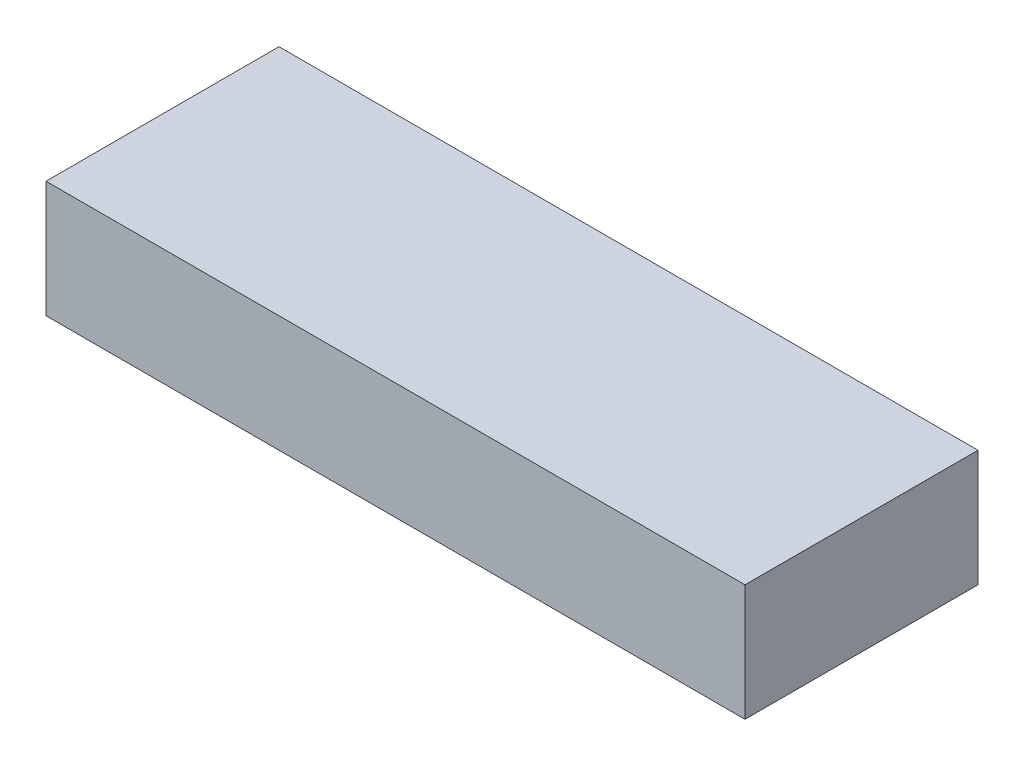
SolidWorks part; units mm, degrees
ref_plane "Front Plane" through (0, 0, 0) normal (0, 0, 1) x (1, 0, 0)
ref_plane "Top Plane" through (0, 0, 0) normal (0, 1, 0) x (1, 0, 0)
ref_plane "Right Plane" through (0, 0, 0) normal (1, 0, 0) x (0, 0, -1)
sketch "Sketch1" plane through (0, 0, 0) normal (0, 1, 0) x (1, 0, 0)
  line L1 (30, 10) -> (-30, 10)
  line L2 (30, 10) -> (30, -10)
  line L3 (30, -10) -> (-30, -10)
  line L4 (-30, 10) -> (-30, -10)
  line L5 (30, 10) -> (-30, -10) construction
  line L6 (30, -10) -> (-30, 10) construction
  point P0 (0, 0)
  dimension "D1" = 60
extrude "Boss-Extrude1" add sketch "Sketch1" along normal blind 10
